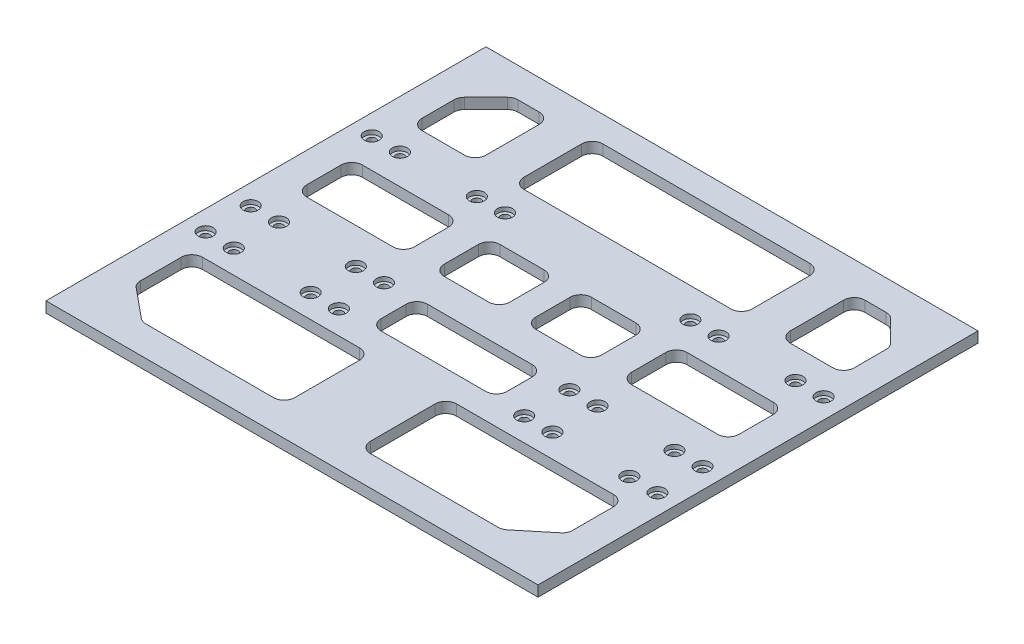
SolidWorks part; units mm, degrees
material "Custom Plastic"
ref_plane "Front Plane" through (0, 0, 0) normal (0, 0, 1) x (1, 0, 0)
ref_plane "Top Plane" through (0, 0, 0) normal (0, 1, 0) x (1, 0, 0)
ref_plane "Right Plane" through (0, 0, 0) normal (1, 0, 0) x (0, 0, -1)
sketch "Sketch1" plane through (0, 0, 0) normal (0, 1, 0) x (1, 0, 0)
  line L1 (-57.5, -51.5) -> (57.5, -51.5)
  line L2 (-57.5, -51.5) -> (-57.5, 51.5)
  line L3 (-57.5, 51.5) -> (57.5, 51.5)
  line L4 (57.5, -51.5) -> (57.5, 51.5)
  line L5 (-57.5, -51.5) -> (57.5, 51.5) construction
  line L6 (-57.5, 51.5) -> (57.5, -51.5) construction
  point P0 (0, 0)
  dimension "D1" = 115
  dimension "D2" = 103
extrude "Boss-Extrude1" add sketch "Sketch1" along normal blind 2.5
sketch "Sketch2" plane through (0, 0, 0) normal (0, -1, 0) x (1, 0, 0)
  line L0 (-57.5, 51.5) -> (57.5, 51.5) construction
  line L1 (-57.5, -51.5) -> (-57.5, 51.5) construction
  line L2 (0, 51.5) -> (0, -51.5) construction
  line L3 (57.5, -51.5) -> (-57.5, -51.5) construction
  line L4 (-46.3, 51.5) -> (-46.3, -51.5) construction
  line L5 (-37.3, -51.5) -> (-37.3, 45.883) construction
  line L6 (-28.3, -51.5) -> (-28.3, 45.883) construction
  circle A0 centre (-52.9, -20.06) radius 1
  circle A1 centre (-52.9, 8.27) radius 1
  circle A2 centre (-52.9, 18.84) radius 1
  circle A3 centre (52.9, -20.06) radius 1
  circle A4 centre (52.9, 8.27) radius 1
  circle A5 centre (52.9, 18.84) radius 1
  circle A6 centre (-46.3, 18.84) radius 1
  circle A7 centre (-46.3, -20.06) radius 1
  circle A8 centre (-46.3, 8.27) radius 1
  circle A9 centre (46.3, -20.06) radius 1
  circle A10 centre (46.3, 8.27) radius 1
  circle A11 centre (46.3, 18.84) radius 1
  circle A12 centre (-28.3, 18.84) radius 1
  circle A13 centre (-21.7, 18.84) radius 1
  circle A14 centre (-21.7, 8.27) radius 1
  circle A15 centre (-28.3, 8.27) radius 1
  circle A16 centre (-21.7, -20.06) radius 1
  circle A17 centre (-28.3, -20.06) radius 1
  circle A18 centre (21.7, 18.84) radius 1
  circle A19 centre (28.3, 18.84) radius 1
  circle A20 centre (28.3, 8.27) radius 1
  circle A21 centre (21.7, 8.27) radius 1
  circle A22 centre (28.3, -20.06) radius 1
  circle A23 centre (21.7, -20.06) radius 1
  dimension "D7" = 2
  dimension "D8" = 2
  dimension "D9" = 2
  dimension "D12" = 2
  dimension "D14" = 2
  dimension "D15" = 43.23
  dimension "D16" = 2
  dimension "D1" = 32.66
  dimension "D2" = 43.23
  dimension "D3" = 71.56
  dimension "D4" = 4.6
  dimension "D5" = 4.6
  dimension "D6" = 4.6
  dimension "D10" = 11.2
  dimension "D11" = 32.66
  dimension "D13" = 71.56
  dimension "D17" = 18
  dimension "D18" = 9
extrude "Cut-Extrude1" cut sketch "Sketch2" against normal blind 10
sketch "Sketch3" plane through (-57.5, 0, 0) normal (-1, 0, 0) x (0, 0, 1)
  line L8 (-51.5, 0) -> (51.5, 0)
  line L9 (51.5, 0) -> (51.5, 2.5)
  line L10 (51.5, 2.5) -> (-51.5, 2.5)
  line L11 (-51.5, 2.5) -> (-51.5, 0)
  line L12 (-51.5, 0) -> (51.5, 0)
  line L13 (51.5, 0) -> (51.5, 2.5)
  line L14 (51.5, 2.5) -> (-51.5, 2.5)
  line L15 (-51.5, 2.5) -> (-51.5, 0)
  dimension "D1" = 0
extrude "Boss-Extrude2" add sketch "Sketch3" along normal blind 0.1
sketch "Sketch4" plane through (57.5, 0, 0) normal (1, 0, 0) x (0, 0, -1)
  line L4 (-51.5, 0) -> (51.5, 0)
  line L5 (51.5, 0) -> (51.5, 2.5)
  line L6 (51.5, 2.5) -> (-51.5, 2.5)
  line L7 (-51.5, 2.5) -> (-51.5, 0)
  line L8 (-51.5, 0) -> (51.5, 0)
  line L9 (51.5, 0) -> (51.5, 2.5)
  line L10 (51.5, 2.5) -> (-51.5, 2.5)
  line L11 (-51.5, 2.5) -> (-51.5, 0)
  dimension "D1" = 0
extrude "Boss-Extrude3" add sketch "Sketch4" along normal blind 0.1
sketch "Sketch6" plane through (0, 2.5, 0) normal (0, 1, 0) x (1, 0, 0)
  line L0 (-44.8762, 43.7678) -> (-49.8678, 38.7762)
  line L1 (-50.6, 37.0084) -> (-50.6, 29.5256)
  line L2 (-48.1, 27.0256) -> (-38.1257, 27.0256)
  line L3 (-35.6257, 29.5256) -> (-35.6257, 42)
  line L4 (-38.1257, 44.5) -> (-43.1084, 44.5)
  line L5 (57.6, 51.5) -> (-57.6, 51.5) construction
  line L6 (0, 64.7841) -> (0, -71.4614) construction
  line L7 (-24.2114, 45.5) -> (24.2114, 45.5)
  line L8 (-26.7114, 43) -> (-26.7114, 29.5256)
  line L9 (-24.2114, 27.0256) -> (24.2114, 27.0256)
  line L10 (26.7114, 43) -> (26.7114, 29.5256)
  line L11 (-49.6888, -38.3001) -> (-42.8486, -43.9302)
  line L12 (-48.1, 0.0564) -> (-27.9271, 0.0564)
  line L13 (-50.6, 2.5564) -> (-50.6, 10.569)
  line L14 (-48.1, 13.069) -> (-27.9271, 13.069)
  line L15 (-25.4271, 2.5564) -> (-25.4271, 10.569)
  line L16 (-50.6, 0.0564) -> (-25.4271, 13.069) construction
  line L17 (-50.6, 13.069) -> (-25.4271, 0.0564) construction
  line L18 (-15.9179, 0.0564) -> (-5.5337, 0.0564)
  line L19 (-18.4179, 2.5564) -> (-18.4179, 10.569)
  line L20 (-15.9179, 13.069) -> (-5.5337, 13.069)
  line L21 (-3.0337, 2.5564) -> (-3.0337, 10.569)
  line L22 (-18.4179, 0.0564) -> (-3.0337, 13.069) construction
  line L23 (-18.4179, 13.069) -> (-3.0337, 0.0564) construction
  line L24 (-41.2598, -44.5) -> (-11.3488, -44.5)
  line L25 (-50.6, -36.3699) -> (-50.6, -26.8363)
  line L26 (-48.1, -24.3363) -> (-11.3488, -24.3363)
  line L27 (-8.8488, -42) -> (-8.8488, -26.8363)
  line L28 (-47.0786, -40.4486) -> (-8.8488, -24.3363) construction
  line L29 (-50.6, -24.3363) -> (-8.8488, -44.5) construction
  line L30 (-57.6, -51.5) -> (-57.6, 51.5) construction
  line L32 (-57.6, -51.5) -> (57.6, -51.5) construction
  line L33 (41.2598, -44.5) -> (11.3488, -44.5)
  line L34 (-12.2501, -18.3965) -> (12.2501, -18.3965)
  line L35 (-14.7501, -15.8965) -> (-14.7501, -10.0236)
  line L36 (-12.2501, -7.5236) -> (12.2501, -7.5236)
  line L37 (14.7501, -15.8965) -> (14.7501, -10.0236)
  line L38 (-14.7501, -18.3965) -> (14.7501, -7.5236) construction
  line L39 (-14.7501, -7.5236) -> (14.7501, -18.3965) construction
  line L40 (8.8488, -42) -> (8.8488, -26.8363)
  line L41 (48.1, -24.3363) -> (11.3488, -24.3363)
  line L42 (50.6, -36.3699) -> (50.6, -26.8363)
  line L43 (49.6888, -38.3001) -> (42.8486, -43.9302)
  line L44 (3.0337, 2.5564) -> (3.0337, 10.569)
  line L45 (15.9179, 13.069) -> (5.5337, 13.069)
  line L46 (18.4179, 2.5564) -> (18.4179, 10.569)
  line L47 (15.9179, 0.0564) -> (5.5337, 0.0564)
  line L48 (48.1, 0.0564) -> (27.9271, 0.0564)
  line L49 (50.6, 2.5564) -> (50.6, 10.569)
  line L50 (48.1, 13.069) -> (27.9271, 13.069)
  line L51 (25.4271, 2.5564) -> (25.4271, 10.569)
  line L52 (48.1, 27.0256) -> (38.1257, 27.0256)
  line L53 (50.6, 37.0084) -> (50.6, 29.5256)
  line L54 (44.8762, 43.7678) -> (49.8678, 38.7762)
  line L55 (38.1257, 44.5) -> (43.1084, 44.5)
  line L56 (35.6257, 29.5256) -> (35.6257, 42)
  arc A0 (-49.8678, 38.7762) -> (-50.6, 37.0084) centre (-48.1, 37.0084) ccw
  arc A1 (-44.8762, 43.7678) -> (-43.1084, 44.5) centre (-43.1084, 42) cw
  arc A2 (-42.8486, -43.9302) -> (-41.2598, -44.5) centre (-41.2598, -42) ccw
  arc A3 (-49.6888, -38.3001) -> (-50.6, -36.3699) centre (-48.1, -36.3699) cw
  arc A4 (-50.6, -26.8363) -> (-48.1, -24.3363) centre (-48.1, -26.8363) cw
  arc A5 (-11.3488, -44.5) -> (-8.8488, -42) centre (-11.3488, -42) ccw
  arc A6 (-11.3488, -24.3363) -> (-8.8488, -26.8363) centre (-11.3488, -26.8363) cw
  arc A7 (12.2501, -7.5236) -> (14.7501, -10.0236) centre (12.2501, -10.0236) cw
  arc A8 (12.2501, -18.3965) -> (14.7501, -15.8965) centre (12.2501, -15.8965) ccw
  arc A9 (-12.2501, -18.3965) -> (-14.7501, -15.8965) centre (-12.2501, -15.8965) cw
  arc A10 (-14.7501, -10.0236) -> (-12.2501, -7.5236) centre (-12.2501, -10.0236) cw
  arc A11 (-27.9271, 13.069) -> (-25.4271, 10.569) centre (-27.9271, 10.569) cw
  arc A12 (-27.9271, 0.0564) -> (-25.4271, 2.5564) centre (-27.9271, 2.5564) ccw
  arc A13 (-48.1, 0.0564) -> (-50.6, 2.5564) centre (-48.1, 2.5564) cw
  arc A14 (-50.6, 10.569) -> (-48.1, 13.069) centre (-48.1, 10.569) cw
  arc A15 (24.2114, 27.0256) -> (26.7114, 29.5256) centre (24.2114, 29.5256) ccw
  arc A16 (24.2114, 45.5) -> (26.7114, 43) centre (24.2114, 43) cw
  arc A17 (-5.5337, 13.069) -> (-3.0337, 10.569) centre (-5.5337, 10.569) cw
  arc A18 (-5.5337, 0.0564) -> (-3.0337, 2.5564) centre (-5.5337, 2.5564) ccw
  arc A19 (-15.9179, 0.0564) -> (-18.4179, 2.5564) centre (-15.9179, 2.5564) cw
  arc A20 (-18.4179, 10.569) -> (-15.9179, 13.069) centre (-15.9179, 10.569) cw
  arc A21 (-24.2114, 45.5) -> (-26.7114, 43) centre (-24.2114, 43) ccw
  arc A22 (-26.7114, 29.5256) -> (-24.2114, 27.0256) centre (-24.2114, 29.5256) ccw
  arc A23 (-38.1257, 27.0256) -> (-35.6257, 29.5256) centre (-38.1257, 29.5256) ccw
  arc A24 (-35.6257, 42) -> (-38.1257, 44.5) centre (-38.1257, 42) ccw
  arc A25 (-50.6, 29.5256) -> (-48.1, 27.0256) centre (-48.1, 29.5256) ccw
  arc A26 (42.8486, -43.9302) -> (41.2598, -44.5) centre (41.2598, -42) cw
  arc A27 (11.3488, -44.5) -> (8.8488, -42) centre (11.3488, -42) cw
  arc A28 (11.3488, -24.3363) -> (8.8488, -26.8363) centre (11.3488, -26.8363) ccw
  arc A29 (50.6, -26.8363) -> (48.1, -24.3363) centre (48.1, -26.8363) ccw
  arc A30 (49.6888, -38.3001) -> (50.6, -36.3699) centre (48.1, -36.3699) ccw
  arc A31 (5.5337, 0.0564) -> (3.0337, 2.5564) centre (5.5337, 2.5564) cw
  arc A32 (5.5337, 13.069) -> (3.0337, 10.569) centre (5.5337, 10.569) ccw
  arc A33 (18.4179, 10.569) -> (15.9179, 13.069) centre (15.9179, 10.569) ccw
  arc A34 (15.9179, 0.0564) -> (18.4179, 2.5564) centre (15.9179, 2.5564) ccw
  arc A35 (27.9271, 13.069) -> (25.4271, 10.569) centre (27.9271, 10.569) ccw
  arc A36 (27.9271, 0.0564) -> (25.4271, 2.5564) centre (27.9271, 2.5564) cw
  arc A37 (48.1, 0.0564) -> (50.6, 2.5564) centre (48.1, 2.5564) ccw
  arc A38 (50.6, 10.569) -> (48.1, 13.069) centre (48.1, 10.569) ccw
  arc A39 (38.1257, 27.0256) -> (35.6257, 29.5256) centre (38.1257, 29.5256) cw
  arc A40 (50.6, 29.5256) -> (48.1, 27.0256) centre (48.1, 29.5256) cw
  arc A41 (49.8678, 38.7762) -> (50.6, 37.0084) centre (48.1, 37.0084) cw
  arc A42 (44.8762, 43.7678) -> (43.1084, 44.5) centre (43.1084, 42) ccw
  arc A43 (35.6257, 42) -> (38.1257, 44.5) centre (38.1257, 42) cw
  point P14 (0, 45.5)
  point P15 (-38.0136, 6.5627)
  point P20 (-10.7258, 6.5627)
  point P26 (-31.1437, -33.7327)
  point P36 (0, -12.9601)
  dimension "D6" = 2.5
  dimension "D1" = 7
  dimension "D2" = 7
  dimension "D3" = 7
  dimension "D4" = 7
  dimension "D5" = 7
extrude "Cut-Extrude3" cut sketch "Sketch6" against normal blind 10
ref_plane "Plane1" through (0, 0, 0) normal (-1, 0, 0) x (0, 0, 1)
sketch "Sketch7" plane through (0, 2.5, 0) normal (0, 1, 0) x (1, 0, 0)
  line L0 (0, 51.5) -> (0, -52.1311) construction
  line L1 (57.6, 51.5) -> (-57.6, 51.5) construction
  line L2 (-37.3, 51.5) -> (-37.3, -51.5) construction
  line L3 (-57.6, -51.5) -> (57.6, -51.5) construction
  circle A0 centre (-52.9, 20.06) radius 1.75
  circle A1 centre (-46.3, 20.06) radius 1.75
  circle A2 centre (-52.9, -8.27) radius 1.75
  circle A3 centre (-46.3, -8.27) radius 1.75
  circle A4 centre (-52.9, -18.84) radius 1.75
  circle A5 centre (-46.3, -18.84) radius 1.75
  circle A6 centre (-28.3, -18.84) radius 1.75
  circle A7 centre (-21.7, -18.84) radius 1.75
  circle A8 centre (-28.3, -8.27) radius 1.75
  circle A9 centre (-21.7, -8.27) radius 1.75
  circle A10 centre (-21.7, 20.06) radius 1.75
  circle A11 centre (-28.3, 20.06) radius 1.75
  circle A12 centre (21.7, -18.84) radius 1.75
  circle A13 centre (28.3, -18.84) radius 1.75
  circle A14 centre (46.3, -18.84) radius 1.75
  circle A15 centre (52.9, -18.84) radius 1.75
  circle A16 centre (21.7, -8.27) radius 1.75
  circle A17 centre (28.3, -8.27) radius 1.75
  circle A18 centre (46.3, -8.27) radius 1.75
  circle A19 centre (52.9, -8.27) radius 1.75
  circle A20 centre (21.7, 20.06) radius 1.75
  circle A21 centre (28.3, 20.06) radius 1.75
  circle A22 centre (46.3, 20.06) radius 1.75
  circle A23 centre (52.9, 20.06) radius 1.75
  dimension "D1" = 3.5
  dimension "D2" = 3.5
  dimension "D3" = 3.5
  dimension "D4" = 3.5
  dimension "D5" = 3.5
  dimension "D6" = 3.5
  dimension "D7" = 9
extrude "Cut-Extrude4" cut sketch "Sketch7" against normal blind 1
